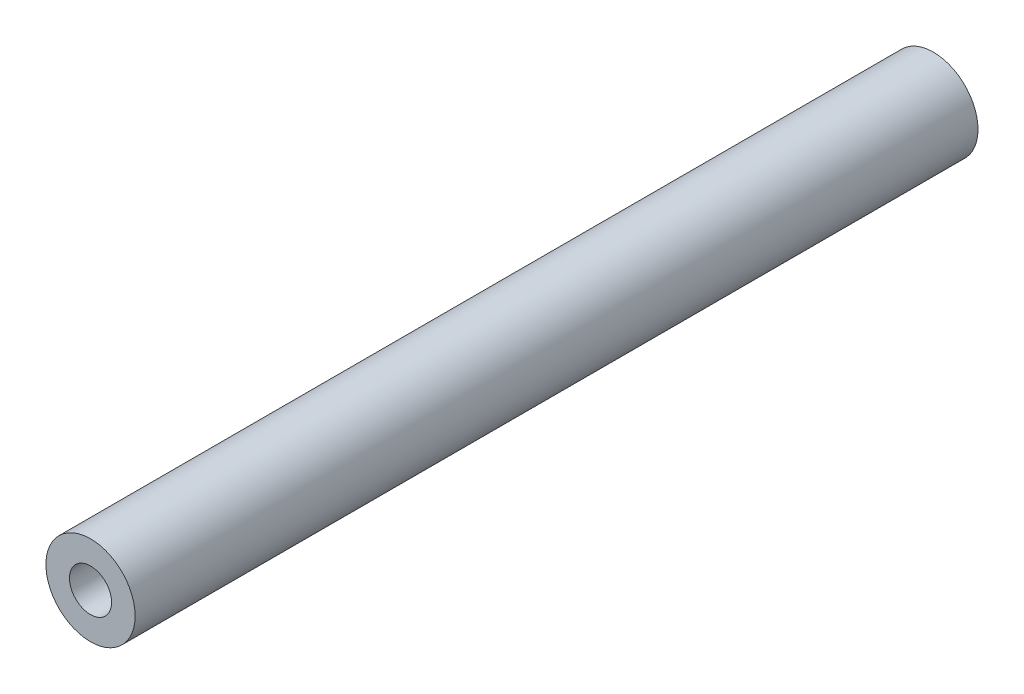
SolidWorks part; units mm, degrees
ref_plane "Front Plane" through (0, 0, 0) normal (0, 0, 1) x (1, 0, 0)
ref_plane "Top Plane" through (0, 0, 0) normal (0, 1, 0) x (1, 0, 0)
ref_plane "Right Plane" through (0, 0, 0) normal (1, 0, 0) x (0, 0, -1)
sketch "Sketch1" plane through (0, 0, 0) normal (0, 0, 1) x (1, 0, 0)
  circle A0 centre (0, 0) radius 1.5875
  dimension "D1" = 3.175
extrude "Boss-Extrude1" add sketch "Sketch1" along normal offset from surface 6.35 and the other way offset from surface (31.304 mm away) 1.5875
sketch "Sketch2" plane through (0, 0, -31.304) normal (0, 0, -1) x (-1, 0, 0)
  circle A1 centre (0, 0) radius 1.5875
  circle A2 centre (0, 0) radius 1.5875
  dimension "D1" = 0
extrude "Cut-Extrude1" cut sketch "Sketch2" against normal offset from surface (7.654 mm away) 30 up to face at (1.5875, 0, 6.35)
sketch "Sketch3" plane through (0, 0, 6.35) normal (0, 0, 1) x (1, 0, 0)
  circle A0 centre (0, 0) radius 0.75
extrude "Cut-Extrude2" cut sketch "Sketch3" against normal blind 12.7 draft 1
